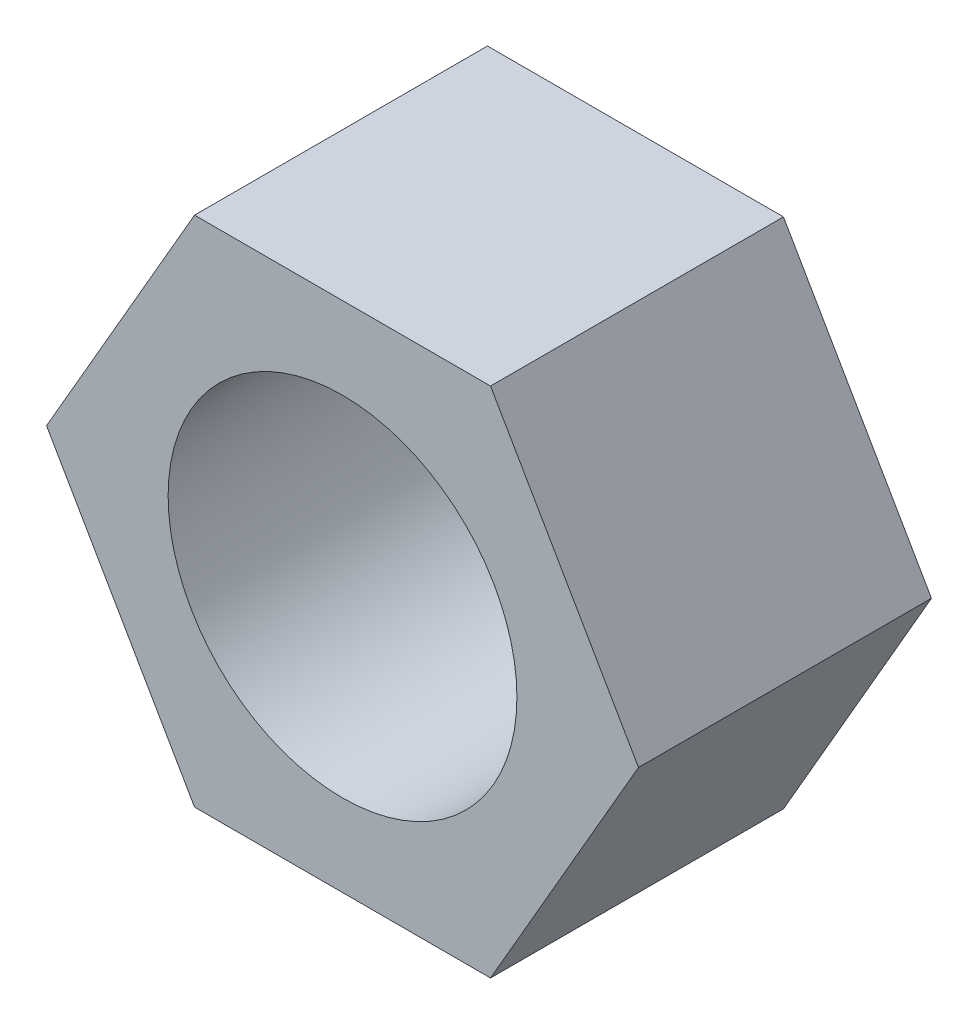
SolidWorks part; units mm, degrees
ref_plane "Front Plane" through (0, 0, 0) normal (0, 0, 1) x (1, 0, 0)
ref_plane "Top Plane" through (0, 0, 0) normal (0, 1, 0) x (1, 0, 0)
ref_plane "Right Plane" through (0, 0, 0) normal (1, 0, 0) x (0, 0, -1)
sketch "Sketch1" plane through (0, 0, 0) normal (0, 0, 1) x (1, 0, 0)
  line L1 (8.0829, 0) -> (4.0415, 7)
  line L2 (4.0415, 7) -> (-4.0415, 7)
  line L3 (-4.0415, 7) -> (-8.0829, 0)
  line L4 (-8.0829, 0) -> (-4.0415, -7)
  line L5 (-4.0415, -7) -> (4.0415, -7)
  line L6 (4.0415, -7) -> (8.0829, 0)
  circle A0 centre (0, 0) radius 7 construction
extrude "Boss-Extrude1" add sketch "Sketch1" along normal blind 8
sketch "Sketch2" plane through (0, 0, 0) normal (0, 0, -1) x (-1, 0, 0)
  circle A0 centre (0, 0) radius 4.7625
  dimension "D1" = 9.525
extrude "Cut-Extrude1" cut sketch "Sketch2" against normal blind 8
